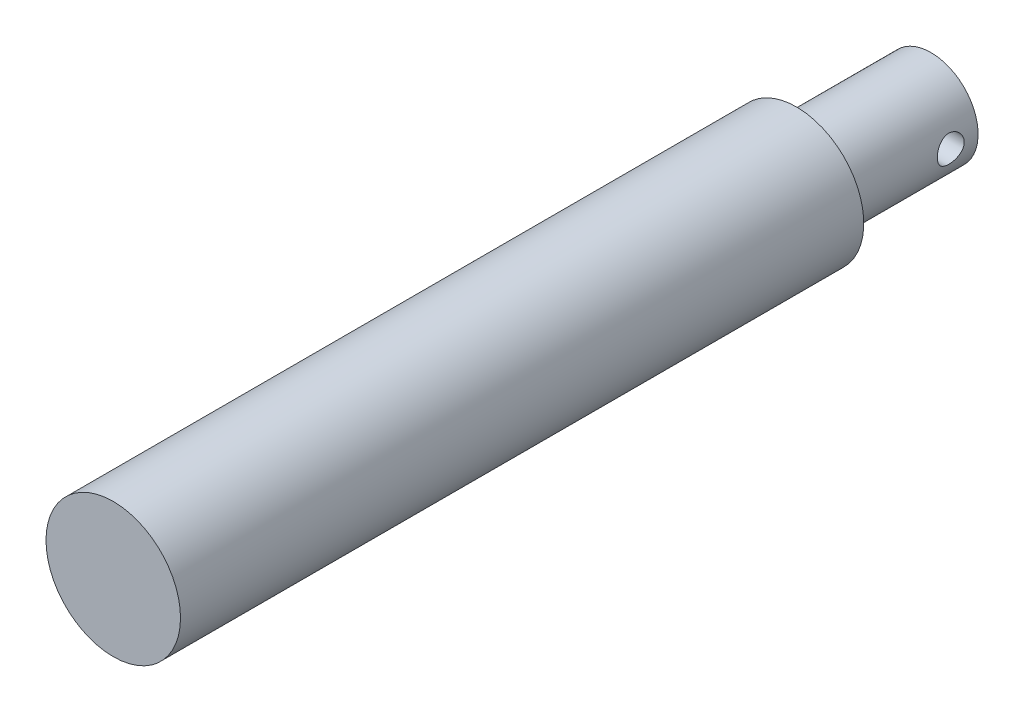
SolidWorks part; units mm, degrees
ref_plane "Front Plane" through (0, 0, 0) normal (0, 0, 1) x (1, 0, 0)
ref_plane "Top Plane" through (0, 0, 0) normal (0, 1, 0) x (1, 0, 0)
ref_plane "Right Plane" through (0, 0, 0) normal (1, 0, 0) x (0, 0, -1)
sketch "Sketch1" plane through (0, 0, 0) normal (0, 0, 1) x (1, 0, 0)
  circle A0 centre (0, 0) radius 5
extrude "Boss-Extrude1" add sketch "Sketch1" along normal blind 60.8
sketch "Sketch2" plane through (0, 0, 0) normal (1, 0, 0) x (0, 0, -1)
  line L0 (0, -5) -> (0, 5) construction
  circle A0 centre (-2.0314, 0) radius 1
  dimension "D1" = 2
  dimension "D2" = 2.0314
extrude "Cut-Extrude1" cut sketch "Sketch2" against normal through all and the other way through all
sketch "Sketch3" plane through (0, 0, 0) normal (0, 0, -1) x (-1, 0, 0)
  circle A0 centre (0, 0) radius 3.5
  dimension "D1" = 7
extrude "Cut-Extrude2" cut sketch "Sketch3" against normal blind 10 flip side to cut
